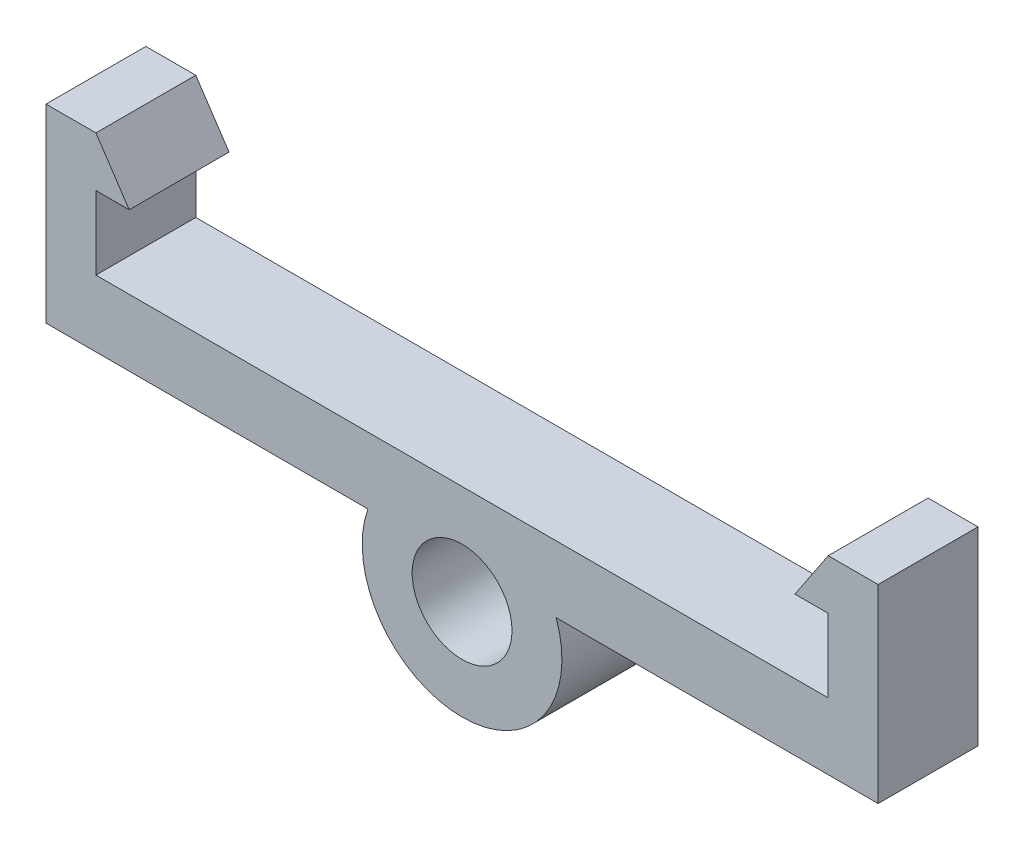
SolidWorks part; units mm, degrees
ref_plane "Ebene vorne" through (0, 0, 0) normal (0, 0, 1) x (1, 0, 0)
ref_plane "Ebene oben" through (0, 0, 0) normal (0, 1, 0) x (1, 0, 0)
ref_plane "Ebene rechts" through (0, 0, 0) normal (1, 0, 0) x (0, 0, -1)
sketch "Skizze1" plane through (0, 0, 0) normal (0, 0, 1) x (1, 0, 0)
  line L0 (-12.5, 5.2) -> (-12.5, -0.5)
  line L1 (-12.5, -0.5) -> (-2.8284, -0.5)
  line L2 (0, -1.5) -> (0, 1.5) construction
  line L3 (11, 1.5) -> (-11, 1.5)
  line L4 (-11, 1.5) -> (-11, 3.7)
  line L5 (-11, 3.7) -> (-10, 3.7)
  line L6 (-10, 3.7) -> (-11, 5.2)
  line L7 (-11, 5.2) -> (-12.5, 5.2)
  line L8 (11, 5.2) -> (12.5, 5.2)
  line L9 (10, 3.7) -> (11, 5.2)
  line L10 (11, 3.7) -> (10, 3.7)
  line L11 (11, 1.5) -> (11, 3.7)
  line L12 (12.5, 5.2) -> (12.5, -0.5)
  line L17 (2.8284, -0.5) -> (12.5, -0.5)
  circle A0 centre (0, -1.5) radius 1.5
  arc A1 (-2.8284, -0.5) -> (2.8284, -0.5) centre (0, -1.5) ccw
  point P22 (0, -4.5)
  dimension "D7" = 3
  dimension "D8" = 3
  dimension "D1" = 22
  dimension "D2" = 1
  dimension "D3" = 1.5
  dimension "D4" = 2
  dimension "D5" = 2.2
  dimension "D6" = 1.5
  dimension "D9" = 6
extrude "Aufsatz-Linear austragen1" add sketch "Skizze1" along normal mid plane 3
